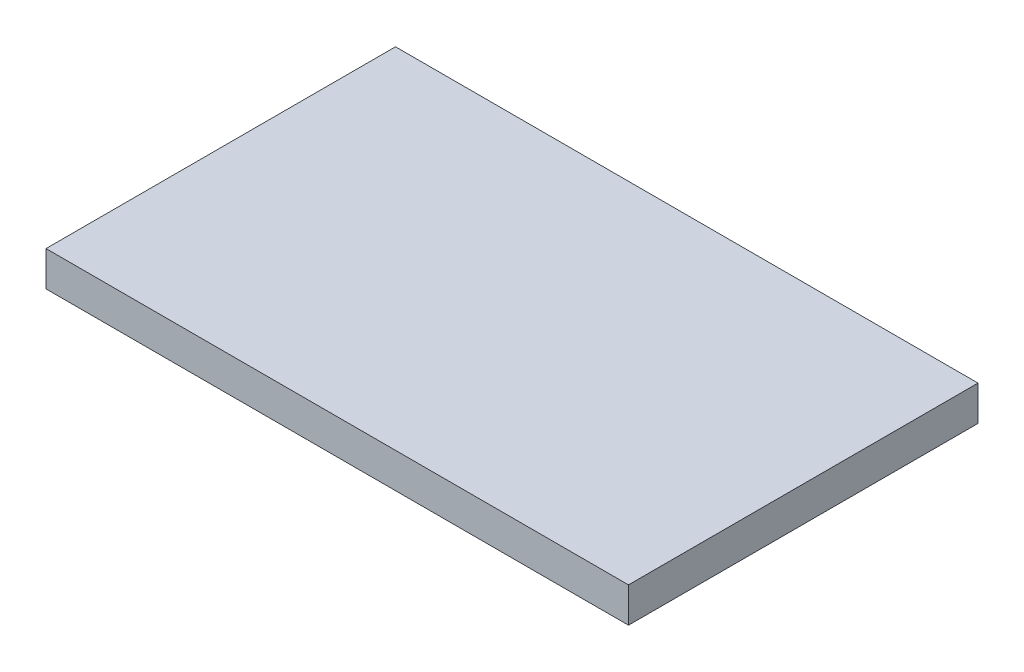
SolidWorks part; units mm, degrees
ref_plane "Front Plane" through (0, 0, 0) normal (0, 0, 1) x (1, 0, 0)
ref_plane "Top Plane" through (0, 0, 0) normal (0, 1, 0) x (1, 0, 0)
ref_plane "Right Plane" through (0, 0, 0) normal (1, 0, 0) x (0, 0, -1)
sketch "Sketch1" plane through (0, 0, 0) normal (0, 1, 0) x (1, 0, 0)
  line L1 (-25, -15) -> (25, -15)
  line L2 (-25, -15) -> (-25, 15)
  line L3 (-25, 15) -> (25, 15)
  line L4 (25, -15) -> (25, 15)
  line L5 (-25, -15) -> (25, 15) construction
  line L6 (-25, 15) -> (25, -15) construction
  point P0 (0, 0)
  dimension "D1" = 30
  dimension "D2" = 50
extrude "Boss-Extrude1" add sketch "Sketch1" along normal blind 3
